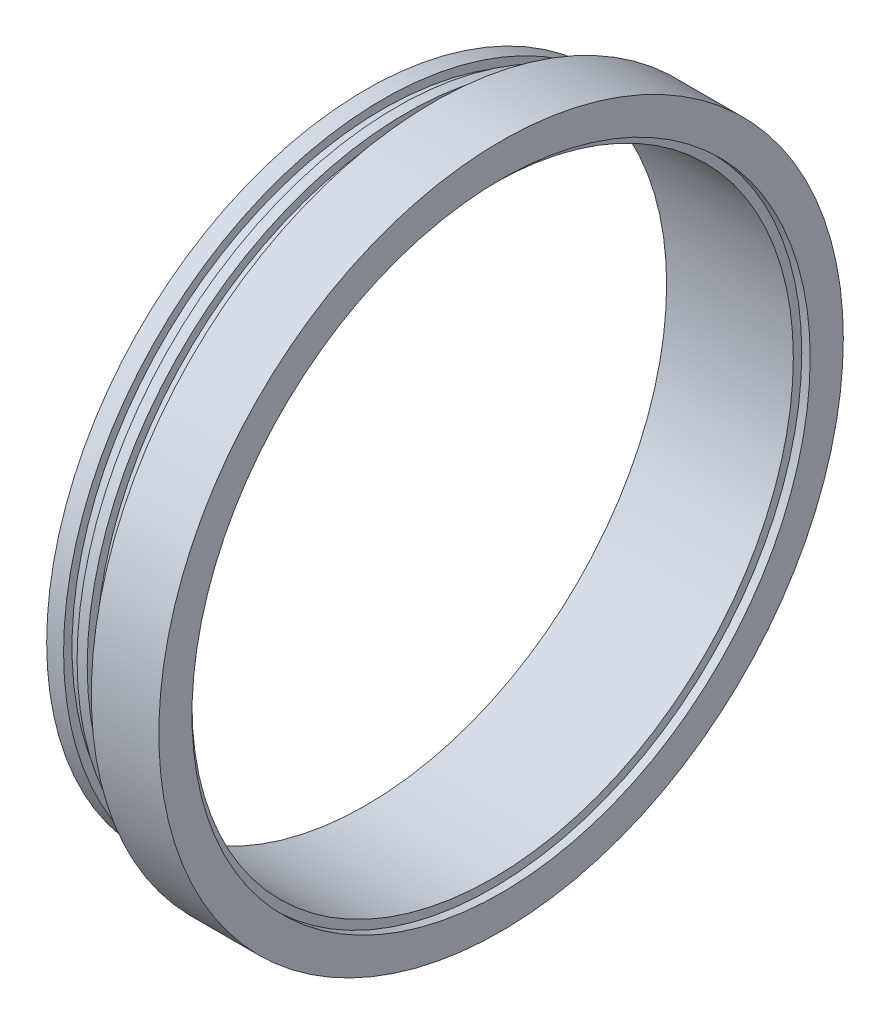
SolidWorks part; units mm, degrees
ref_plane "Front Plane" through (0, 0, 0) normal (0, 0, 1) x (1, 0, 0)
ref_plane "Top Plane" through (0, 0, 0) normal (0, 1, 0) x (1, 0, 0)
ref_plane "Right Plane" through (0, 0, 0) normal (1, 0, 0) x (0, 0, -1)
sketch "Sketch1" plane through (0, 0, 0) normal (0, 0, 1) x (1, 0, 0)
  line L1 (0, 89) -> (37.5, 89)
  line L2 (0, 89) -> (0, 94.5)
  line L3 (0, 94.5) -> (5, 94.5)
  line L4 (5, 94.5) -> (5, 92)
  line L5 (5, 92) -> (9, 92)
  line L6 (9, 92) -> (9, 94.5)
  line L7 (9, 94.5) -> (12, 94.5)
  line L8 (12, 94.5) -> (12, 92)
  line L9 (12, 92) -> (16, 92)
  line L10 (16, 92) -> (16, 94.5)
  line L11 (16, 94.5) -> (20, 94.5)
  line L12 (20, 94.5) -> (20, 101.3)
  line L13 (20, 101.3) -> (40, 101.3)
  line L14 (40, 101.3) -> (40, 91.5)
  line L15 (37.5, 89) -> (37.5, 91.5)
  line L16 (37.5, 91.5) -> (40, 91.5)
  dimension "D1" = 94.5
  dimension "D2" = 89
ref_axis "Axis1" through (42, 0, 0) along (-1, 0, 0)
revolve "Revolve1" add sketch "Sketch1" angle 360 about axis through (42, 0, 0) along (-1, 0, 0)
